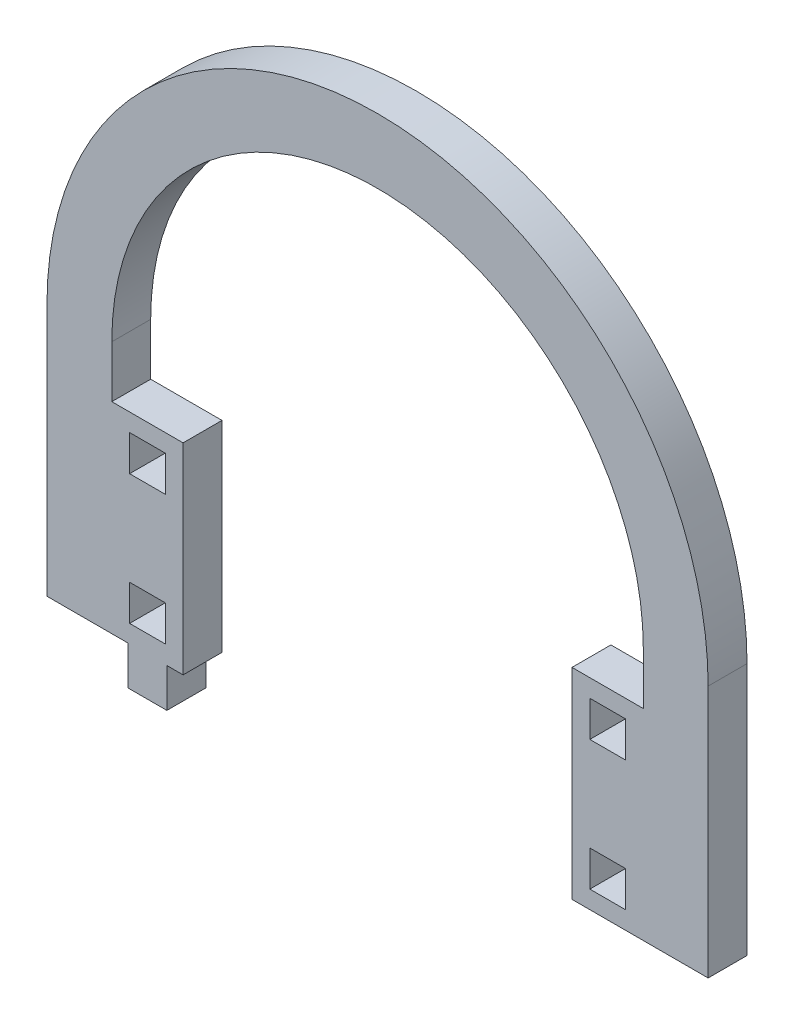
SolidWorks part; units mm, degrees
ref_plane "Front Plane" through (0, 0, 0) normal (0, 0, 1) x (1, 0, 0)
ref_plane "Top Plane" through (0, 0, 0) normal (0, 1, 0) x (1, 0, 0)
ref_plane "Right Plane" through (0, 0, 0) normal (1, 0, 0) x (0, 0, -1)
sketch "Model" plane through (0, 0, 0) normal (0, 0, 1) x (1, 0, 0)
  line L0 (2982.6124, 1260.8088) -> (2982.6124, 1221.8088)
  line L1 (3074.6124, 1221.8088) -> (3084.6124, 1221.8088)
  line L2 (3084.6124, 1260.8088) -> (3084.6124, 1221.8088)
  line L3 (3074.6124, 1260.8088) -> (3074.6124, 1252.8088)
  line L4 (2992.6124, 1260.8088) -> (2992.6124, 1252.8088)
  line L5 (3071.8624, 1230.0588) -> (3066.3624, 1230.0588)
  line L6 (3066.3624, 1230.0588) -> (3066.3624, 1224.5588)
  line L7 (3066.3624, 1224.5588) -> (3071.8624, 1224.5588)
  line L8 (3071.8624, 1224.5588) -> (3071.8624, 1230.0588)
  line L9 (3063.6124, 1221.8088) -> (3074.6124, 1221.8088)
  line L10 (3071.8624, 1250.0588) -> (3066.3624, 1250.0588)
  line L11 (3066.3624, 1250.0588) -> (3066.3624, 1244.5588)
  line L12 (3066.3624, 1244.5588) -> (3071.8624, 1244.5588)
  line L13 (3071.8624, 1244.5588) -> (3071.8624, 1250.0588)
  line L14 (3074.6124, 1252.8088) -> (3063.6124, 1252.8088)
  line L15 (3000.8624, 1230.0588) -> (2995.3624, 1230.0588)
  line L16 (2995.3624, 1230.0588) -> (2995.3624, 1224.5588)
  line L17 (2995.3624, 1224.5588) -> (3000.8624, 1224.5588)
  line L18 (3000.8624, 1224.5588) -> (3000.8624, 1230.0588)
  line L19 (3001.1124, 1221.8088) -> (3003.6124, 1221.8088)
  line L20 (2995.1124, 1221.8088) -> (2995.1124, 1215.8088)
  line L21 (2995.1124, 1215.8088) -> (3001.1124, 1215.8088)
  line L22 (3001.1124, 1215.8088) -> (3001.1124, 1221.8088)
  line L23 (3000.8624, 1250.0588) -> (2995.3624, 1250.0588)
  line L24 (2995.3624, 1250.0588) -> (2995.3624, 1244.5588)
  line L25 (2995.3624, 1244.5588) -> (3000.8624, 1244.5588)
  line L26 (3000.8624, 1244.5588) -> (3000.8624, 1250.0588)
  line L27 (3003.6124, 1252.8088) -> (2992.6124, 1252.8088)
  line L28 (3003.6124, 1252.8088) -> (3003.6124, 1221.8088)
  line L29 (3063.6124, 1252.8088) -> (3063.6124, 1221.8088)
  line L30 (2982.6124, 1221.8088) -> (2995.1124, 1221.8088)
  arc A0 (3084.6124, 1260.8088) -> (2982.6124, 1260.8088) centre (3033.6124, 1260.8088) ccw
  arc A1 (3074.6124, 1260.8088) -> (2992.6124, 1260.8088) centre (3033.6124, 1260.8088) ccw
extrude "Boss-Extrude1" add sketch "Model" along normal blind 6 contours L17 L18 L15 L16 | L12 L13 L10 L11 | L7 L8 L5 L6 | L0 L30 L20 L21 L22 L19 L28 L27 L4 A1 L3 L14 L29 L9 L1 L2 A0 | L25 L26 L23 L24
